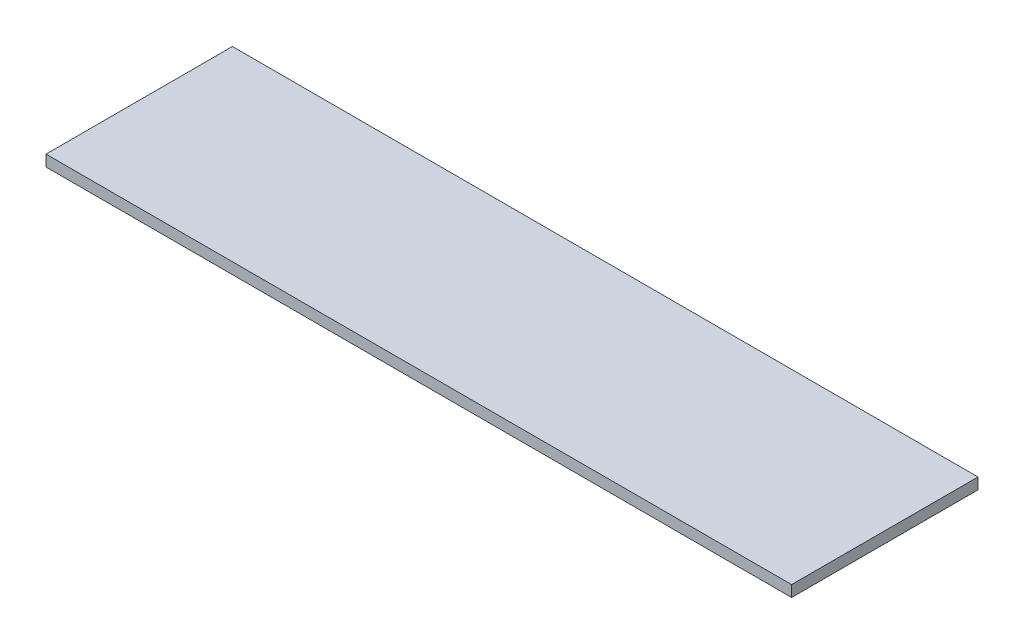
SolidWorks part; units mm, degrees
ref_plane "Спереди" through (0, 0, 0) normal (0, 0, 1) x (1, 0, 0)
ref_plane "Сверху" through (0, 0, 0) normal (0, 1, 0) x (1, 0, 0)
ref_plane "Справа" through (0, 0, 0) normal (1, 0, 0) x (0, 0, -1)
sketch "Эскиз1" plane through (0, 0, 0) normal (0, 1, 0) x (1, 0, 0)
  line L1 (-50, 12.5) -> (50, 12.5)
  line L2 (-50, 12.5) -> (-50, -12.5)
  line L3 (-50, -12.5) -> (50, -12.5)
  line L4 (50, 12.5) -> (50, -12.5)
  line L5 (-50, 12.5) -> (50, -12.5) construction
  line L6 (-50, -12.5) -> (50, 12.5) construction
  point P0 (0, 0)
extrude "Бобышка-Вытянуть1" add sketch "Эскиз1" along normal blind 1.5
